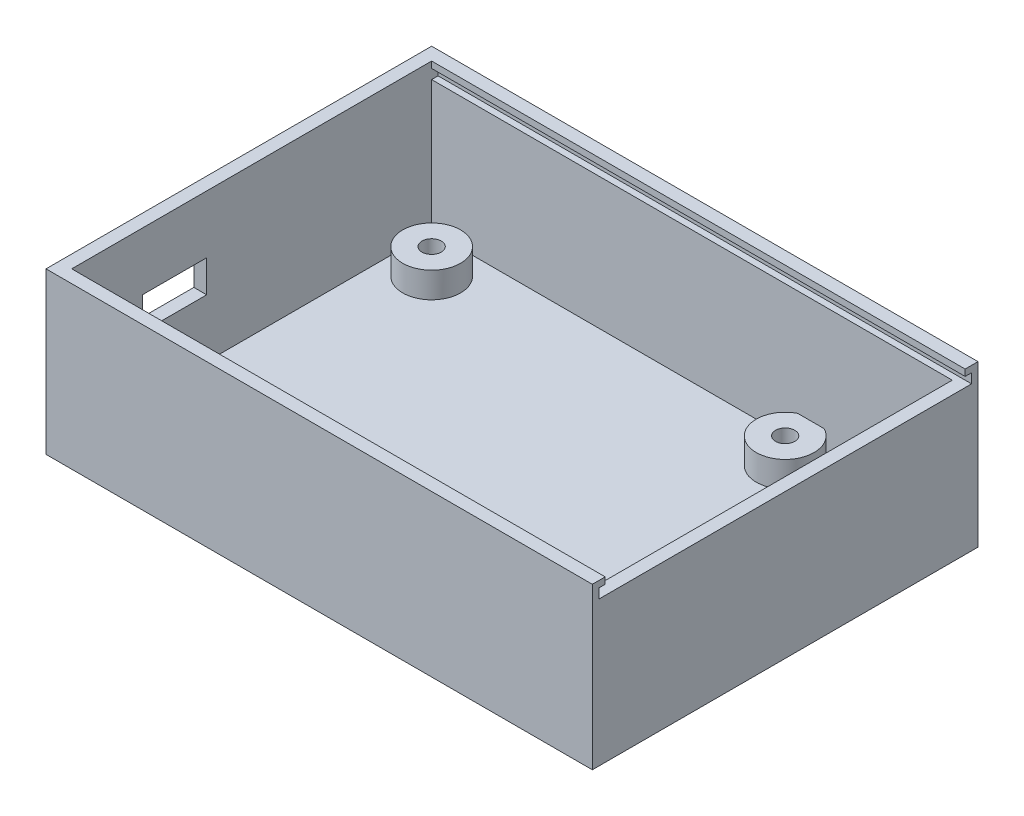
SolidWorks part; units mm, degrees
ref_plane "Ebene vorne" through (0, 0, 0) normal (0, 0, 1) x (1, 0, 0)
ref_plane "Ebene oben" through (0, 0, 0) normal (0, 1, 0) x (1, 0, 0)
ref_plane "Ebene rechts" through (0, 0, 0) normal (1, 0, 0) x (0, 0, -1)
sketch "Skizze1" plane through (0, 0, 0) normal (0, 1, 0) x (1, 0, 0)
  line L1 (0, 0) -> (85, 0)
  line L2 (0, 0) -> (0, 60)
  line L3 (0, 60) -> (85, 60)
  line L4 (85, 0) -> (85, 60)
  dimension "D1" = 85
  dimension "D2" = 60
extrude "Aufsatz-Linear austragen1" add sketch "Skizze1" along normal blind 25
shell "Wandung1" thickness 2
sketch "Skizze2" plane through (0, 2, 0) normal (0, 1, 0) x (1, 0, 0)
  line L0 (2, 58) -> (2, 2) construction
  line L1 (83, 58) -> (2, 58) construction
  circle A0 centre (8, 52) radius 1.5
  circle A1 centre (8, 52) radius 4.5
  circle A2 centre (61, 54) radius 1.5
  circle A3 centre (61, 54) radius 4.5
  circle A4 centre (68, 13) radius 1.5
  circle A5 centre (68, 13) radius 4.5
  dimension "D3" = 3
  dimension "D4" = 3
  dimension "D7" = 3
  dimension "D8" = 3
  dimension "D11" = 3
  dimension "D12" = 3
  dimension "D1" = 6
  dimension "D2" = 6
  dimension "D5" = 4
  dimension "D6" = 53
  dimension "D9" = 41
  dimension "D10" = 7
extrude "Aufsatz-Linear austragen2" add sketch "Skizze2" along normal blind 4
sketch "Skizze3" plane through (0, 0, 0) normal (-1, 0, 0) x (0, 0, 1)
  line L0 (-60, 0) -> (0, 0) construction
  line L1 (-23, 11) -> (-13, 11)
  line L2 (-23, 11) -> (-23, 16)
  line L3 (-23, 16) -> (-13, 16)
  line L4 (-13, 11) -> (-13, 16)
  line L5 (0, 25) -> (0, 0) construction
  dimension "D1" = 16
  dimension "D2" = 5
  dimension "D3" = 10
  dimension "D4" = 13
extrude "Schnitt-Linear austragen1" cut sketch "Skizze3" against normal up to next
sketch "Skizze4" plane through (85, 0, 0) normal (1, 0, 0) x (0, 0, -1)
  line L0 (0, 25) -> (60, 25) construction
  line L1 (2, 25) -> (58, 25)
  line L2 (2, 25) -> (2, 24)
  line L3 (2, 24) -> (58, 24)
  line L4 (58, 25) -> (58, 24)
  line L5 (0, 25) -> (0, 0) construction
  line L6 (60, 25) -> (60, 0) construction
  dimension "D1" = 2
  dimension "D2" = 2
  dimension "D3" = 1
sketch "Skizze5" plane through (85, 0, 0) normal (1, 0, 0) x (0, 0, -1)
  line L0 (0, 25) -> (0, 0) construction
  line L1 (1, 22.5) -> (59, 22.5)
  line L2 (1, 22.5) -> (1, 24)
  line L3 (1, 24) -> (59, 24)
  line L4 (59, 22.5) -> (59, 24)
  line L5 (60, 25) -> (60, 0) construction
  line L6 (2, 25) -> (58, 25) construction
  dimension "D1" = 1
  dimension "D2" = 1
  dimension "D3" = 1.5
  dimension "D4" = 1
extrude "Schnitt-Linear austragen2" cut sketch "Skizze4" against normal up to next
extrude "Schnitt-Linear austragen3" cut sketch "Skizze5" against normal up to surface (83 mm away) up to face at (2, 13.5, -18)
